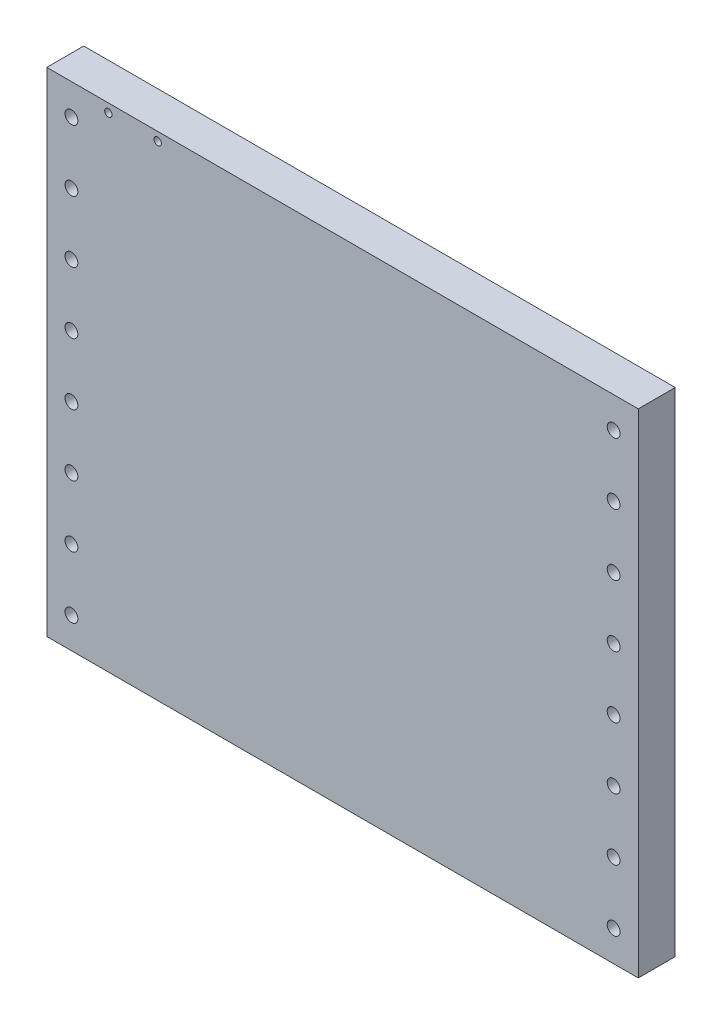
SolidWorks part; units mm, degrees
ref_plane "Front Plane" through (0, 0, 0) normal (0, 0, 1) x (1, 0, 0)
ref_plane "Top Plane" through (0, 0, 0) normal (0, 1, 0) x (1, 0, 0)
ref_plane "Right Plane" through (0, 0, 0) normal (1, 0, 0) x (0, 0, -1)
sketch "Sketch1" plane through (0, 0, 0) normal (0, 0, 1) x (1, 0, 0)
  line L1 (-120, -100) -> (120, -100)
  line L2 (-120, -100) -> (-120, 100)
  line L3 (-120, 100) -> (120, 100)
  line L4 (120, -100) -> (120, 100)
  line L5 (-120, -100) -> (120, 100) construction
  line L6 (-120, 100) -> (120, -100) construction
  point P0 (0, 0)
  dimension "D1" = 240
  dimension "D2" = 200
extrude "Boss-Extrude1" add sketch "Sketch1" along normal mid plane 15
sketch "Sketch4" plane through (0, 0, 7.5) normal (0, 0, 1) x (1, 0, 0)
  line L0 (-110, -1033.7087) -> (-110, 48966.2913) construction
  line L1 (110, -1052.3781) -> (110, 48947.6219) construction
  line L2 (-1012.9649, 87.5) -> (48987.0351, 87.5) construction
  line L4 (-120, 100) -> (-120, -100) construction
  line L5 (120, -100) -> (120, 100) construction
  line L6 (120, 100) -> (-120, 100) construction
  circle A0 centre (-110, 87.5) radius 2.6
  circle A1 centre (110, 87.5) radius 2.6
  dimension "D4" = 5.2
  dimension "D5" = 5.2
  dimension "D1" = 12.5
  dimension "D2" = 10
  dimension "D3" = 10
extrude "Cut-Extrude3" cut sketch "Sketch4" against normal through all
pattern_linear "LPattern1" count 8 spacing 25 along (0, -1, 0) of "Cut-Extrude3"
sketch "Sketch3" [suppressed] plane through (0, 7.5, 0) normal (0, 1, 0) x (1, 0, 0)
  line L1 (-92.5, -105) -> (92.5, -105)
  line L2 (-97.5, -100) -> (-97.5, 100)
  line L3 (-92.5, 105) -> (92.5, 105)
  line L4 (97.5, -100) -> (97.5, 100)
  line L5 (-97.5, -105) -> (97.5, 105) construction
  line L6 (-97.5, 105) -> (97.5, -105) construction
  arc A0 (-92.5, -105) -> (-97.5, -100) centre (-92.5, -100) cw
  arc A1 (97.5, -100) -> (92.5, -105) centre (92.5, -100) cw
  arc A2 (97.5, 100) -> (92.5, 105) centre (92.5, 100) ccw
  arc A3 (-92.5, 105) -> (-97.5, 100) centre (-92.5, 100) ccw
  point P0 (0, 0)
  dimension "D3" = 5
  dimension "D1" = 195
  dimension "D2" = 210
sketch "Sketch5" plane through (0, 0, 7.5) normal (0, 0, 1) x (1, 0, 0)
  line L0 (120, 100) -> (-120, 100) construction
  line L1 (-120, 100) -> (-120, -100) construction
  circle A0 centre (-95, 96.5) radius 1.5
  circle A1 centre (-75, 96.5) radius 1.5
  dimension "D1" = 3
  dimension "D2" = 3
  dimension "D3" = 20
  dimension "D4" = 3.5
  dimension "D5" = 25
  dimension "D6" = 3.5
extrude "Cut-Extrude4" cut sketch "Sketch5" against normal through all
